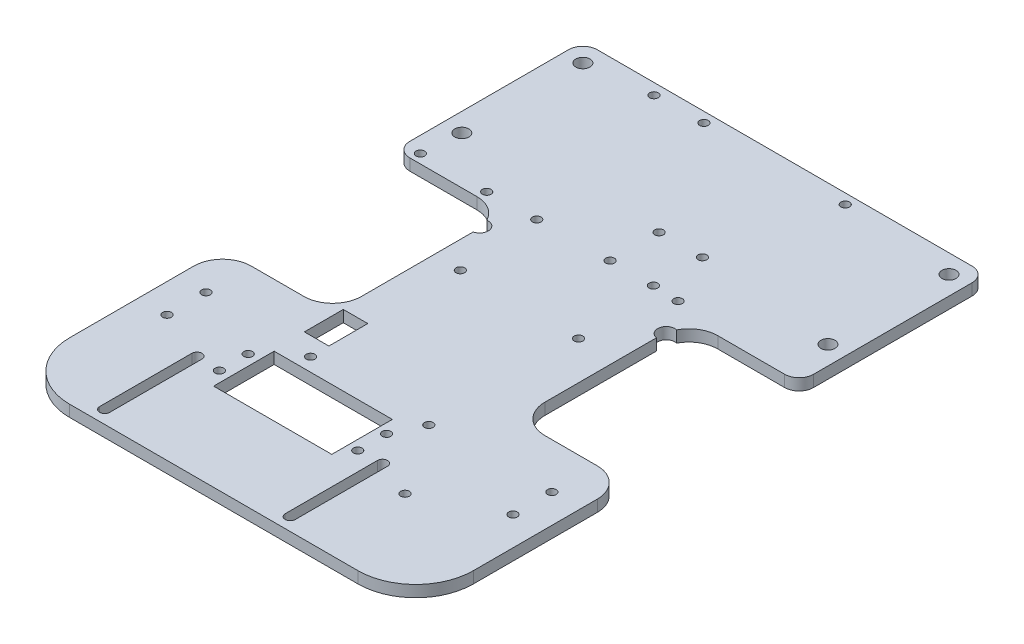
SolidWorks part; units mm, degrees
ref_plane "Front Plane" through (0, 0, 0) normal (0, 0, 1) x (1, 0, 0)
ref_plane "Top Plane" through (0, 0, 0) normal (0, 1, 0) x (1, 0, 0)
ref_plane "Right Plane" through (0, 0, 0) normal (1, 0, 0) x (0, 0, -1)
sketch "Sketch1" plane through (0, 0, 0) normal (0, 1, 0) x (1, 0, 0)
  line L0 (-120, 0) -> (-135, 0)
  line L19 (-20, 0) -> (-120, 0)
  line L20 (0, -20) -> (0, -178)
  line L21 (-20, -198) -> (-120, -198)
  line L22 (-140, -20) -> (-140, -178)
  line L23 (-140, -5) -> (-140, -20)
  line L24 (-20, 0) -> (-5, 0)
  line L25 (0, -5) -> (0, -20)
  arc A27 (-120, -198) -> (-140, -178) centre (-120, -178) cw
  arc A28 (0, -178) -> (-20, -198) centre (-20, -178) cw
  arc A31 (-5, 0) -> (0, -5) centre (-5, -5) cw
  arc A32 (-135, 0) -> (-140, -5) centre (-135, -5) ccw
  point P9 (0, -198)
  point P12 (0, 0)
  point P15 (-140, 0)
  point P17 (0, 0)
  point P20 (-140, 0)
  dimension "D1" = 140
  dimension "D2" = 198
  dimension "D4" = 5
  dimension "D3" = 20
extrude "Boss-Extrude1" add sketch "Sketch1" along normal blind 4
sketch "Sketch2" plane through (0, 4, 0) normal (0, 1, 0) x (1, 0, 0)
  line L0 (-70, 0) -> (-70, -53.3557) construction
  line L5 (-5, 0) -> (-135, 0) construction
  line L22 (-112.3765, -161.5) -> (-112.3765, -193.5) construction
  line L23 (-110.6265, -161.5) -> (-110.6265, -193.5)
  line L31 (-114.1265, -161.5) -> (-114.1265, -193.5)
  line L36 (-100.4906, -167.6056) -> (-59.4906, -167.6056)
  line L37 (-100.4906, -167.6056) -> (-100.4906, -146.6056)
  line L38 (-100.4906, -146.6056) -> (-59.4906, -146.6056)
  line L39 (-59.4906, -167.6056) -> (-59.4906, -146.6056)
  line L40 (-48, -161.5) -> (-48, -193.5) construction
  line L43 (-101.0411, -122.0681) -> (-92.5411, -122.0681)
  line L44 (-101.0411, -122.0681) -> (-101.0411, -135.5681)
  line L45 (-46.25, -161.5) -> (-46.25, -193.5)
  line L46 (-49.75, -161.5) -> (-49.75, -193.5)
  line L47 (-120, -198) -> (-20, -198) construction
  line L48 (-101.0411, -135.5681) -> (-92.5411, -135.5681)
  line L49 (-92.5411, -122.0681) -> (-92.5411, -135.5681)
  circle A4 centre (-6.5, -6.5) radius 2.45
  circle A5 centre (-6.5, -48.5) radius 2.45
  circle A6 centre (-133.5, -48.5) radius 2.45
  circle A7 centre (-133.5, -6.5) radius 2.45
  circle A42 centre (-130, -140.75) radius 1.5
  circle A43 centre (-130, -154.25) radius 1.5
  circle A44 centre (-10, -154.25) radius 1.5
  circle A45 centre (-10, -140.75) radius 1.5
  arc A56 (-110.6265, -161.5) -> (-114.1265, -161.5) centre (-112.3765, -161.5) ccw
  circle A57 centre (-69.4148, -44.133) radius 1.5
  arc A68 (-114.1265, -193.5) -> (-110.6265, -193.5) centre (-112.3765, -193.5) ccw
  arc A69 (-46.25, -161.5) -> (-49.75, -161.5) centre (-48, -161.5) ccw
  arc A70 (-49.75, -193.5) -> (-46.25, -193.5) centre (-48, -193.5) ccw
  circle A75 centre (-112.3765, -165.7764) radius 1.5 construction
  circle A76 centre (-48, -165.7764) radius 1.5 construction
  circle A77 centre (-104.1511, -151.9482) radius 1.5
  circle A78 centre (-104.1511, -161.9482) radius 1.5
  circle A79 centre (-56.1511, -161.9482) radius 1.5
  circle A80 centre (-54.4148, -44.133) radius 1.5
  circle A81 centre (-54.4148, -61.133) radius 1.5
  circle A82 centre (-69.4148, -61.133) radius 1.5
  circle A83 centre (-51.5001, -90.0161) radius 1.5
  circle A86 centre (-51.5001, -141.9482) radius 1.5
  circle A87 centre (-56.1511, -151.9482) radius 1.5
  circle A88 centre (-92.5001, -141.9482) radius 1.5
  circle A89 centre (-92.5001, -90.0161) radius 1.5
  circle A93 centre (-45.5, -61.5) radius 1.5
  circle A94 centre (-45.5, -3.5) radius 1.5
  circle A95 centre (-94.5, -3.5) radius 1.5
  circle A96 centre (-94.5, -61.5) radius 1.5
  circle A97 centre (-111.4972, -3.8646) radius 1.5
  circle A98 centre (-111.4972, -61.8646) radius 1.5
  circle A99 centre (-134.4972, -61.8646) radius 1.5
  circle A102 centre (-34.9586, -166.731) radius 1.5
  point P4 (-59.4906, -157.1056)
  point P5 (-100.4906, -157.1056)
  point P6 (-79.9906, -146.6056)
  point P67 (-112.3765, -177.5)
  point P76 (-48, -177.5)
  dimension "D1" = 10.5
  dimension "D2" = 4.5
  dimension "D3" = 4.5
  dimension "D4" = 16
  dimension "D5" = 10.5
  dimension "D6" = 20.5
  dimension "D7" = 16
extrude "Cut-Extrude1" cut sketch "Sketch2" against normal through all both and the other way through all
sketch "Sketch3" plane through (0, 0, 0) normal (0, -1, 0) x (-1, 0, 0)
  line L0 (0, -178) -> (0, -5) construction
  line L1 (0, -65) -> (28.2086, -65)
  line L2 (0, -65) -> (0, -125)
  line L3 (0, -125) -> (28.2086, -125)
  line L5 (70, 0) -> (70, -19.6212) construction
  line L6 (5, 0) -> (135, 0) construction
  line L7 (140, -65) -> (140, -125)
  line L8 (140, -65) -> (111.7914, -65)
  line L10 (140, -125) -> (111.7914, -125)
  line L11 (38.2086, -115) -> (38.2086, -76.2698)
  line L12 (101.7914, -115) -> (101.7914, -76.2698)
  arc A0 (28.2086, -125) -> (38.2086, -115) centre (28.2086, -115) ccw
  arc A1 (28.2086, -65) -> (37.0785, -70.382) centre (28.2086, -75) cw
  arc A2 (111.7914, -65) -> (102.9215, -70.382) centre (111.7914, -75) ccw
  arc A3 (111.7914, -125) -> (101.7914, -115) centre (111.7914, -115) cw
  arc A4 (37.0785, -70.382) -> (38.2086, -76.2698) centre (37.7604, -73.3035) cw
  arc A5 (102.9215, -70.382) -> (101.7914, -76.2698) centre (102.4733, -73.3483) ccw
  dimension "D1" = 10
  dimension "D4" = 3
  dimension "D5" = 3
  dimension "D6" = 10
  dimension "D7" = 10
  dimension "D2" = 60
  dimension "D3" = 65
extrude "Cut-Extrude2" cut sketch "Sketch3" against normal through all both and the other way through all
fillet "Fillet1" radius 10 2 edges at (0, 2, 125) (-140, 2, 125)
fillet "Fillet2" radius 5 2 edges at (-140, 2, 65) (0, 2, 65)
